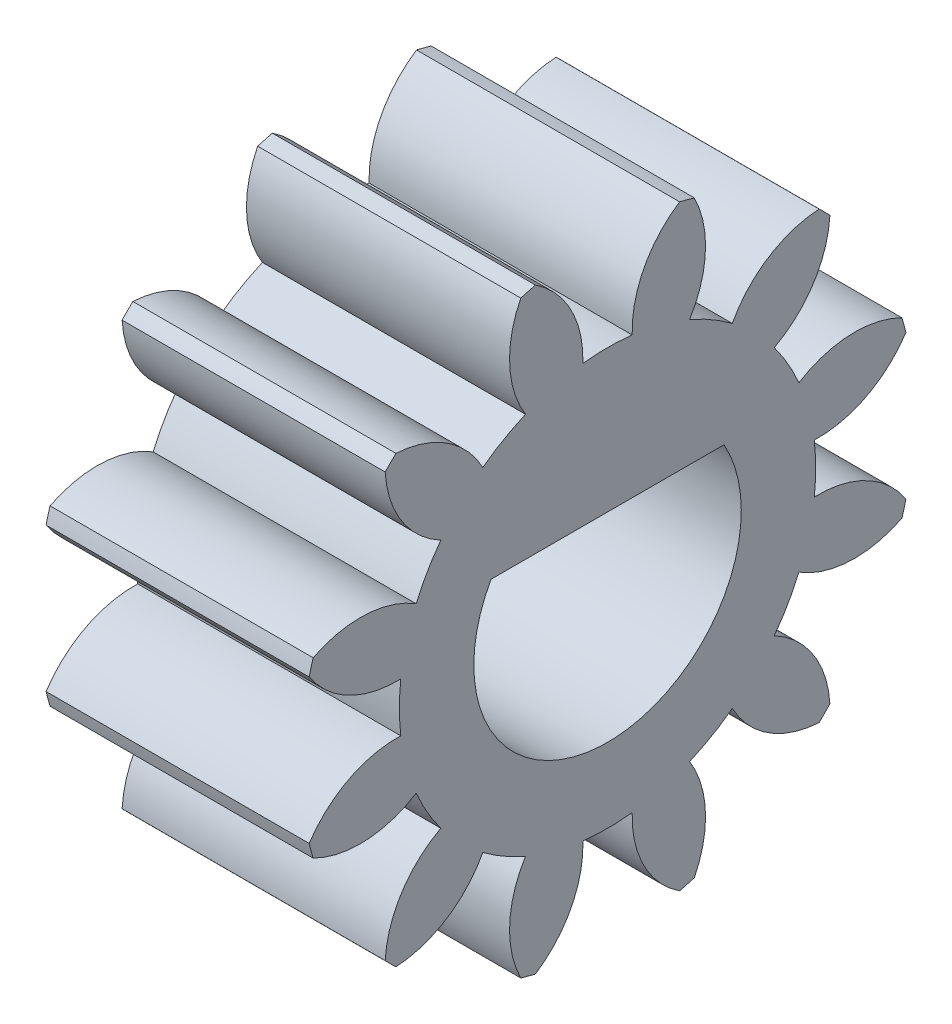
SolidWorks part; units mm, degrees
ref_plane "Plane1" through (0, 0, 0) normal (0, 0, 1) x (1, 0, 0)
ref_plane "Plane2" through (0, 0, 0) normal (0, 1, 0) x (1, 0, 0)
ref_plane "Plane3" through (0, 0, 0) normal (1, 0, 0) x (0, 0, -1)
sketch "HoldingSke" plane through (0, 0, 0) normal (0, 1, 0) x (1, 0, 0)
  line L0 (0, 0) -> (0.9781, -0.2079)
  line L1 (-15, 0) -> (100, 0) construction
  line L2 (0, 0) -> (-2.1039, 2.3779)
  line L3 (0, 0) -> (-11.863, 4.5341)
  line L4 (0, 0) -> (8.4473, 1.7955)
  line L5 (0, 0) -> (-46.8476, -17.4728)
  line L6 (0, 0) -> (-5.8027, -3.9151)
  line L7 (-2.1039, 2.3779) -> (8.6586, 51.2059)
  line L8 (-76.2, 54.61) -> (-76.1, 54.61)
  line L9 (-71.009, 38.7566) -> (-53.1078, 45.2721)
  line L10 (-76.2, 71.12) -> (104.1128, 71.12)
  line L11 (0, 0) -> (-7, 0)
  line L12 (-76.2, 101.6) -> (-76.162, 101.6)
  line L13 (24.9733, 27.94) -> (52.9518, 28.4284)
  line L14 (24.9733, 27.94) -> (24.9743, 27.94)
  line L15 (24.9733, 27.94) -> (100.4006, 29.5858)
  line L16 (-63.627, -1) -> (-12.827, -1)
  circle A0 centre (0, 0) radius 0.4
  circle A1 centre (0, 0) radius 4.749
  circle A2 centre (0, 0) radius 37.5
  circle A3 centre (0, 0) radius 0.4
  dimension "MHD" = 9.498
  dimension "Hub_dia" = 75
  dimension "Bore" = 0.8
  dimension "MBD" = 0.8
  dimension "Num_teeth" = 12
  dimension "Pitch_radius" = 180.3128
  dimension "Pitch" = 1
  dimension "Width" = 7
  dimension "Overall_len" = 50
  dimension "Show_teeth" = 12
  dimension "Thickness" = 7
  dimension "OAL" = 50.0001
  dimension "T_dim" = 0.1
  dimension "Ap" = 20
  dimension "H" = 19.05
  dimension "Backlash" = 0.038
  dimension "Addendum_fac" = 1
  dimension "Dedendum_fac" = 1.25
  dimension "Clearance_fac" = 0.25
  dimension "Dedendum_add" = 0.001
  dimension "Module" = 1
sketch "BasProSke" plane through (0, 0, 0) normal (0, 1, 0) x (1, 0, 0)
  line L0 (-10, 0) -> (60, 0) construction
  line L1 (0, 0) -> (0, 7)
  line L2 (0, 0) -> (7, 0)
  line L3 (7, 0) -> (7, 7)
  line L4 (7, 7) -> (0, 7)
  dimension "Diameter" = 14
  dimension "Thickness" = 7
revolve "Base-Revolve" add sketch "BasProSke" angle 360 about L0
sketch "TooCutSke" plane through (0, 0, 0) normal (1, 0, 0) x (0, 0, -1)
  line L1 (0, 0) -> (0, 107) construction
  line L2 (0, 0) -> (-0.8496, 5.9395) construction
  line L3 (0, 0) -> (-3.0836, 11.5081) construction
  line L4 (-0.8496, 5.9395) -> (-1.5418, 5.7541) construction
  arc A0 (0.5622, 4.7156) -> (-0.5622, 4.7156) centre (0, 0) ccw
  arc A1 (1.6729, 6.8233) -> (-1.6729, 6.8233) centre (0, 0) ccw
  circle A2 centre (0, 0) radius 6 construction
  circle A3 centre (0, 0) radius 5.6382 construction
  arc A4 (-0.5622, 4.7156) -> (-1.6729, 6.8233) centre (-2.9608, 4.7982) ccw
  arc A5 (1.6729, 6.8233) -> (0.5622, 4.7156) centre (2.9608, 4.7982) ccw
  dimension "Root_dia" = 9.498
  dimension "Overcut_dia" = 14.0508
  dimension "Pitch_dia" = 12
  dimension "Base_dia" = 11.2763
  dimension "Flank_rad" = 2.4
  dimension "Half_ang" = 15
  dimension "Half_CT" = 0.7167
extrude "ToothCut" cut sketch "TooCutSke" along normal through all
fillet "Breaks" [suppressed] radius 0.02
fillet "RootFillets" [suppressed] radius 0.251
pattern_circular "TeethCuts" count 12 every 30 about axis through (-10, 0, 0) along (1, 0, 0) of "ToothCut", "RootFillets", "Breaks"
sketch "HubNeaOneSke" plane through (0, 0, 0) normal (-1, 0, 0) x (0, 0, 1)
  circle A0 centre (0, 0) radius 4.749
  dimension "Diameter" = 9.498
extrude "HubNearOne" [suppressed] add sketch "HubNeaOneSke" along normal blind 43.0001
sketch "HubNeaBotSke" plane through (0, 0, 0) normal (-1, 0, 0) x (0, 0, 1)
  circle A0 centre (0, 0) radius 4.749
  dimension "Diameter" = 9.498
extrude "HubNearBoth" [suppressed] add sketch "HubNeaBotSke" along normal blind 21.5
ref_plane "FarPln" through (7, 0, 0) normal (1, 0, 0) x (0, 0, -1)
sketch "HubFarSke" plane through (7, 0, 0) normal (1, 0, 0) x (0, 0, -1)
  circle A0 centre (0, 0) radius 4.749
  dimension "Diameter" = 9.498
extrude "HubFar" [suppressed] add sketch "HubFarSke" along normal blind 21.5
sketch "BorSke" plane through (0, 0, 0) normal (1, 0, 0) x (0, 0, -1)
  circle A0 centre (0, 0) radius 0.4
  dimension "Diameter" = 0.8
extrude "Bore" cut sketch "BorSke" along normal mid plane 100.0001
sketch "KeySke" plane through (0, 0, 0) normal (1, 0, 0) x (0, 0, -1)
  line L0 (-0.05, 0) -> (-0.05, 0.5)
  line L1 (-0.05, 0.5) -> (0.05, 0.5)
  line L2 (0.05, 0.5) -> (0.05, 0)
  line L3 (0, 0) -> (0, 34) construction
  line L4 (-0.05, 0) -> (0.05, 0)
  dimension "Offset" = 0.5
  dimension "Width" = 0.1
extrude "Keyway" [suppressed] cut sketch "KeySke" along normal mid plane 100.0001
pattern_circular "Keyway2" [suppressed] count 2 every 90 about axis through (-10, 0, 0) along (1, 0, 0)
sketch "Sketch1" plane through (7, 0, 0) normal (1, 0, 0) x (0, 0, -1)
  line L0 (-2.6557, 1.5) -> (2.6557, 1.5)
  arc A0 (-2.6557, 1.5) -> (2.6557, 1.5) centre (0, 0) ccw
  point P5 (0, -3.05)
  dimension "D1" = 6.1
  dimension "D2" = 4.55
extrude "Cut-Extrude1" cut sketch "Sketch1" against normal through all
sketch "Sketch2" plane through (0, 0, 0) normal (-1, 0, 0) x (0, 0, 1)
  circle A0 centre (0, 0) radius 8.8393
extrude "Cut-Extrude2" cut sketch "Sketch2" against normal blind 1 contours A0
equation "' \"Module@HoldingSke\" = 6.35"
equation "' \"Num_teeth@HoldingSke\" = 12"
equation "' \"Ap@HoldingSke\" =  20"
equation "' \"Width@HoldingSke\" = 0.5 * 25.4"
equation "' \"Hub_dia@HoldingSke\"= 1 * 25.4"
equation "' \"Overall_len@HoldingSke\" = 1.0 * 25.4"
equation "' \"Bore@HoldingSke\" = 0.75 * 25.4"
equation "' \"T_dim@HoldingSke\" = 0.1 * 25.4"
equation "' \"Width@KeySke\" = 0.25 * 25.4"
equation "' \"Show_teeth@HoldingSke\" = 13"
equation "' \"Backlash@HoldingSke\" = 0.009 * 25.4"
equation "' \"Addendum_fac@HoldingSke\" = 1.0"
equation "' \"Dedendum_fac@HoldingSke\" = 1.25"
equation "' \"Dedendum_add@HoldingSke\" = 0.00005 * 25.4"
equation "' \"Clearance_fac@HoldingSke\" = 0.25"
equation "\"Pitch@HoldingSke\" = 1 / \"Module@HoldingSke\""
equation "\"Overcut_dia@TooCutSke\" = (\"Num_teeth@HoldingSke\" + 2 * \"Addendum_fac@HoldingSke\") / \"Pitch@HoldingSke\" + 0.002 * 25.4"
equation "\"Pitch_dia@TooCutSke\" = \"Num_teeth@HoldingSke\" / \"Pitch@HoldingSke\""
equation "\"Base_dia@TooCutSke\" = \"Num_teeth@HoldingSke\" / \"Pitch@HoldingSke\" * cos((\"Ap@HoldingSke\"  * 3.14159265 / 180))"
equation "\"Root_dia@TooCutSke\" = (\"Num_teeth@HoldingSke\" + 2) / \"Pitch@HoldingSke\" - 2 * (\"Addendum_fac@HoldingSke\" + \"Dedendum_fac@HoldingSke\") / \"Pitch@HoldingSke\" - \"Dedendum_add@HoldingSke\" * 2"
equation "\"Half_ang@TooCutSke\" = 180 / \"Num_teeth@HoldingSke\""
equation "\"Half_CT@TooCutSke\" = \"Num_teeth@HoldingSke\" / \"Pitch@HoldingSke\" * sin((3.14159265 / 2 / \"Num_teeth@HoldingSke\")) / 2 - 7 * \"Backlash@HoldingSke\" / 4"
equation "\"Flank_rad@TooCutSke\" = \"Num_teeth@HoldingSke\" / \"Pitch@HoldingSke\" / 5"
equation "\"Radius@RootFillets\" = \"Clearance_fac@HoldingSke\" / \"Pitch@HoldingSke\" + \"Dedendum_add@HoldingSke\""
equation "\"Break_rad@Breaks\" = 0.02 / \"Pitch@HoldingSke\""
equation "\"Thickness@HoldingSke\" = \"Width@HoldingSke\""
equation "\"OAL@HoldingSke\" = \"Thickness@HoldingSke\""
equation "\"MHD@HoldingSke\" = (\"Num_teeth@HoldingSke\" + 2) / \"Pitch@HoldingSke\" - 2 * (\"Addendum_fac@HoldingSke\" + \"Dedendum_fac@HoldingSke\")  / \"Pitch@HoldingSke\" - \"Dedendum_add@HoldingSke\" * 2"
equation "\"MBD@HoldingSke\" = (\"Num_teeth@HoldingSke\" + 2) / \"Pitch@HoldingSke\" - 2 * (\"Addendum_fac@HoldingSke\" + \"Dedendum_fac@HoldingSke\")  / \"Pitch@HoldingSke\" - \"Dedendum_add@HoldingSke\" * 2 - 0.002 * 25.4"
equation "\"MHD@HoldingSke\" = ((sgn( \"MHD@HoldingSke\" - \"Hub_dia@HoldingSke\" )-1)*( \"MHD@HoldingSke\" - \"Hub_dia@HoldingSke\" ))/-2+ \"Hub_dia@HoldingSke\""
equation "\"MBD@HoldingSke\" = ((sgn( \"MBD@HoldingSke\" - \"Bore@HoldingSke\" )-1)*( \"MBD@HoldingSke\" - \"Bore@HoldingSke\" ))/-2+ \"Bore@HoldingSke\""
equation "\"OAL@HoldingSke\" = ((sgn( \"OAL@HoldingSke\" - \"Overall_len@HoldingSke\" )+1)*( \"OAL@HoldingSke\" - \"Overall_len@HoldingSke\" ))/2 + \"Overall_len@HoldingSke\" + 0.000002 * 25.4"
equation "\"Num_teeth@TeethCuts\" = int( \"Show_teeth@HoldingSke\" ) + 1"
equation "\"Num_teeth@TeethCuts\" = ((sgn( \"Num_teeth@TeethCuts\" - \"Num_teeth@HoldingSke\" )-1)*( \"Num_teeth@TeethCuts\" - \"Num_teeth@HoldingSke\" ))/-2+ \"Num_teeth@HoldingSke\""
equation "\"Num_teeth@TeethCuts\" = ((sgn( \"Num_teeth@TeethCuts\" - 2.0)+1)*( \"Num_teeth@TeethCuts\" - 2.0))/2 +2.0"
equation "\"Angle@TeethCuts\" = 360.0 / \"Num_teeth@HoldingSke\""
equation "\"Diameter@BasProSke\" = (\"Num_teeth@HoldingSke\" + 2 * \"Addendum_fac@HoldingSke\") / \"Pitch@HoldingSke\""
equation "\"Thickness@BasProSke\"  = \"Thickness@HoldingSke\""
equation "' \"Fillet_rad@BasProSke\" =  \"Thickness@HoldingSke\" * 0.05"
equation "\"MHD@HoldingSke\" = ((sgn( \"MHD@HoldingSke\" - \"Root_dia@TooCutSke\" )-1)*( \"MHD@HoldingSke\" - \"Root_dia@TooCutSke\" ))/-2+ \"Root_dia@TooCutSke\""
equation "\"Diameter@HubNeaOneSke\" = \"MHD@HoldingSke\""
equation "\"Length@HubNearOne\" = \"OAL@HoldingSke\" - \"Thickness@BasProSke\""
equation "\"Diameter@HubNeaBotSke\" = \"MHD@HoldingSke\""
equation "\"Length@HubNearBoth\" = ( \"OAL@HoldingSke\" - \"Thickness@BasProSke\" ) / 2.0"
equation "\"Thickness@FarPln\" = \"Thickness@BasProSke\""
equation "\"Diameter@HubFarSke\" = \"MHD@HoldingSke\""
equation "\"Length@HubFar\" = ( \"OAL@HoldingSke\" - \"Thickness@BasProSke\" ) / 2.0"
equation "\"Diameter@BorSke\" = \"MBD@HoldingSke\""
equation "\"D1@Bore\" = \"OAL@HoldingSke\" * 2.0"
equation "\"D1@Keyway\" = \"OAL@HoldingSke\" * 2.0"
equation "\"Offset@KeySke\" = \"T_dim@HoldingSke\" + \"MBD@HoldingSke\" / 2.0"
